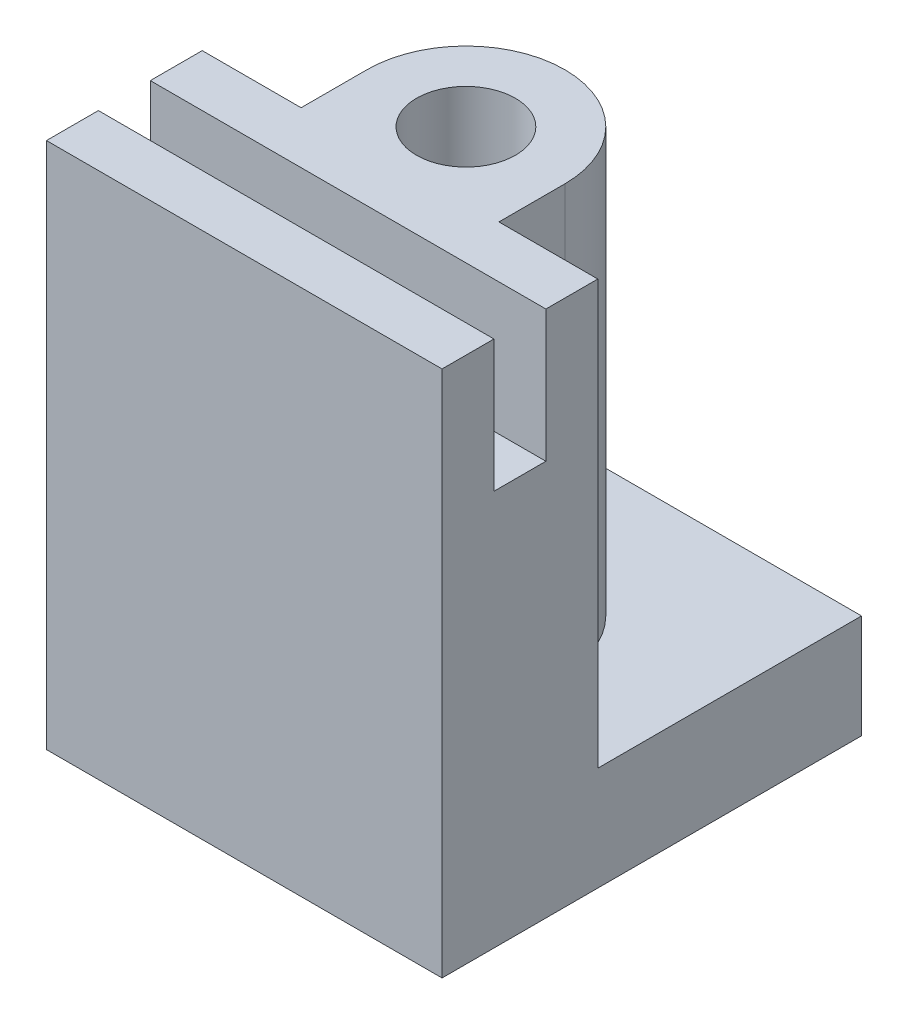
SolidWorks part; units mm, degrees
material "ABS"
ref_plane "Front Plane" through (0, 0, 0) normal (0, 0, 1) x (1, 0, 0)
ref_plane "Top Plane" through (0, 0, 0) normal (0, 1, 0) x (1, 0, 0)
ref_plane "Right Plane" through (0, 0, 0) normal (1, 0, 0) x (0, 0, -1)
sketch "Sketch1" plane through (0, 0, 0) normal (1, 0, 0) x (0, 0, -1)
  line L0 (0, 0) -> (40.4, 0)
  line L1 (40.4, 0) -> (40.4, 10)
  line L2 (40.4, 10) -> (15, 10)
  line L3 (15, 10) -> (15, 50.8)
  line L4 (15, 50.8) -> (10, 50.8)
  line L5 (10, 50.8) -> (10, 38.1)
  line L6 (10, 38.1) -> (5, 38.1)
  line L7 (5, 38.1) -> (5, 50.8)
  line L8 (5, 50.8) -> (0, 50.8)
  line L9 (0, 50.8) -> (0, 0)
  dimension "D1" = 5
  dimension "D2" = 5
  dimension "D3" = 5
  dimension "D4" = 10
  dimension "D5" = 25.4
  dimension "D6" = 12.7
  dimension "D7" = 0
  dimension "D8" = 38.1
extrude "Boss-Extrude1" add sketch "Sketch1" along normal blind 38.1
sketch "Sketch2" plane through (0, 50.8, 0) normal (0, 1, 0) x (1, 0, 0)
  line L0 (9.525, 21.35) -> (9.525, 15)
  line L1 (38.1, 15) -> (0, 15) construction
  line L2 (9.525, 15) -> (28.575, 15)
  line L3 (38.1, 15) -> (0, 15) construction
  line L4 (28.575, 15) -> (28.575, 21.35)
  line L5 (0, 15) -> (38.1, 15) construction
  line L6 (38.1, 40.4) -> (38.1, 15) construction
  arc A0 (9.525, 21.35) -> (28.575, 21.35) centre (19.05, 21.35) cw
  circle A1 centre (19.05, 21.35) radius 4.7625
  point P16 (19.05, 15)
  dimension "D1" = 9.525
  dimension "D2" = 4.7625
  dimension "D3" = 38.1
  dimension "D4" = 19.05
  dimension "D5" = 6.35
extrude "Boss-Extrude2" add sketch "Sketch2" against normal up to next
equation "\"D8@Sketch1\"=1.5in"
equation "\"D1@Boss-Extrude1\"=1.5in"
equation "\"D6@Sketch1\"=.5in"
equation "\"D5@Sketch1\"=1in"
equation "\"D1@Sketch2\"=3in/8"
equation "\"D2@Sketch2\"=3in/16"
equation "\"D4@Sketch2\"=\"D3@Sketch2\"/2"
equation "\"D5@Sketch2\"=1in/4"
